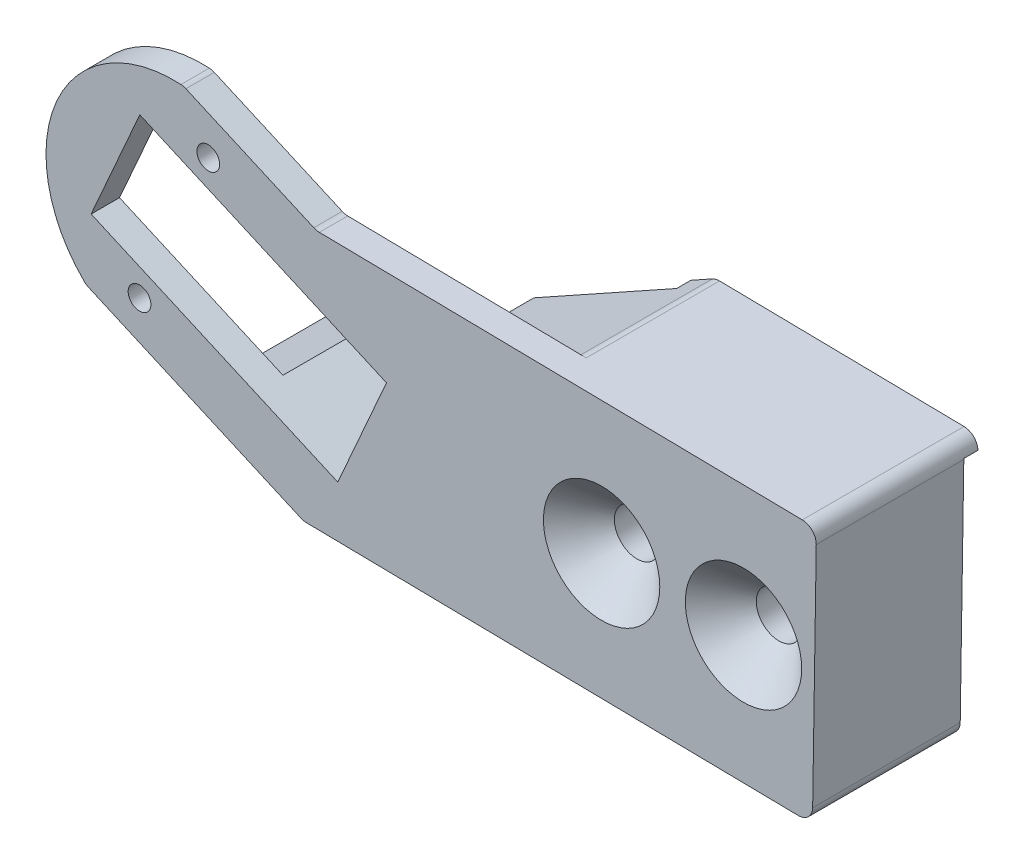
SolidWorks part; units mm, degrees
ref_plane "Front Plane" through (0, 0, 0) normal (0, 0, 1) x (1, 0, 0)
ref_plane "Top Plane" through (0, 0, 0) normal (0, 1, 0) x (1, 0, 0)
ref_plane "Right Plane" through (0, 0, 0) normal (1, 0, 0) x (0, 0, -1)
sketch "Sketch2" plane through (0, 0, 0) normal (0, 0, 1) x (1, 0, 0)
  line L0 (110.8747, 169.3007) -> (232.868, 168.0195) construction
  line L1 (231.4782, 167.9235) -> (111.8685, 169.7952)
  line L2 (109.9284, 170.22) -> (90.3522, 178.8568)
  line L3 (88.0797, 180.8644) -> (81.6243, 191.6546)
  line L4 (91.1154, 198.8867) -> (104.3747, 187.2622)
  line L5 (107.6071, 186.0223) -> (189.9391, 184.9726)
  line L6 (192.2834, 185.5226) -> (216.6587, 198.016)
  line L7 (218.9657, 198.5663) -> (266.2136, 198.3172)
  line L8 (233.9522, 168.5343) -> (269.7006, 188.0491)
  arc A0 (266.2136, 198.3172) -> (269.7006, 188.0491) centre (266.1834, 192.5808) cw
  arc A1 (81.6243, 191.6546) -> (91.1154, 198.8867) centre (86.7764, 194.737) cw
  circle A2 centre (91.5684, 182.2893) radius 1.1478 construction
  circle A3 centre (86.7764, 194.737) radius 1.0668 construction
  circle A4 centre (232.1221, 192.0862) radius 0.8742 construction
  circle A5 centre (266.1834, 192.5808) radius 1.1755 construction
  arc A6 (189.9391, 184.9726) -> (192.2834, 185.5226) centre (190.0028, 189.9722) ccw
  arc A7 (216.6587, 198.016) -> (218.9657, 198.5663) centre (218.9393, 193.5664) cw
  arc A8 (233.9522, 168.5343) -> (231.4782, 167.9235) centre (231.5564, 172.9229) cw
  arc A9 (109.9284, 170.22) -> (111.8685, 169.7952) centre (111.9467, 174.7946) ccw
  arc A10 (107.6071, 186.0223) -> (104.3747, 187.2622) centre (107.6709, 191.0219) cw
  arc A11 (90.3522, 178.8568) -> (88.0797, 180.8644) centre (92.3704, 183.4313) cw
  circle A12 centre (245.4018, 191.4665) radius 0.7725 construction
  circle A13 centre (245.2646, 181.5408) radius 0.6658 construction
  circle A14 centre (208.1864, 183.5188) radius 1.0221 construction
  circle A15 centre (86.7764, 194.737) radius 1.5
  circle A16 centre (91.5684, 182.2893) radius 2
  circle A17 centre (208.1864, 183.5188) radius 1.5
  circle A18 centre (232.1221, 192.0862) radius 1.5
  circle A20 centre (266.1834, 192.5808) radius 2
  dimension "D2" = 4
  dimension "D3" = 3
  dimension "D4" = 3
  dimension "D5" = 4
  dimension "D6" = 3
  dimension "D1" = 122
sketch "Sketch7" plane through (0, 0, 0) normal (0, 0, 1) x (1, 0, 0)
  line L0 (95.6805, 174.2681) -> (100.2651, 184.6595) construction
  line L1 (93.1156, 173.4092) -> (99.1703, 187.1329) construction
  line L2 (93.1156, 173.4092) -> (83.9665, 177.4457)
  line L3 (83.9665, 177.4457) -> (90.0212, 191.1694) construction
  line L4 (99.1703, 187.1329) -> (90.0212, 191.1694)
  line L5 (93.1156, 173.4092) -> (90.0212, 191.1694) construction
  line L6 (83.9665, 177.4457) -> (99.1703, 187.1329) construction
  line L7 (88.541, 175.4274) -> (94.5957, 189.1512) construction
  line L8 (111.8685, 169.7952) -> (231.4782, 167.9235)
  line L9 (233.9522, 168.5343) -> (269.7006, 188.0491)
  line L10 (266.2136, 198.3172) -> (218.9657, 198.5663)
  line L11 (216.6587, 198.016) -> (192.2834, 185.5226)
  line L12 (189.9391, 184.9726) -> (107.6071, 186.0223)
  line L13 (104.3747, 187.2622) -> (91.1154, 198.8867)
  line L14 (81.6243, 191.6546) -> (88.0797, 180.8644)
  line L15 (90.3522, 178.8568) -> (109.9284, 170.22)
  line L16 (111.8685, 169.7952) -> (231.4782, 167.9235) construction
  line L17 (233.9522, 168.5343) -> (269.7006, 188.0491) construction
  line L18 (266.2136, 198.3172) -> (218.9657, 198.5663) construction
  line L19 (216.6587, 198.016) -> (192.2834, 185.5226) construction
  line L20 (189.9391, 184.9726) -> (107.6071, 186.0223) construction
  line L21 (104.3747, 187.2622) -> (91.1154, 198.8867) construction
  line L22 (81.6243, 191.6546) -> (88.0797, 180.8644) construction
  line L23 (90.3522, 178.8568) -> (109.9284, 170.22) construction
  line L24 (86.9938, 184.3075) -> (96.143, 180.2711) construction
  line L25 (100.7006, 168.9698) -> (92.5965, 172.5452)
  line L26 (136.8555, 186.5959) -> (86.8555, 187.3783) construction
  line L27 (136.8555, 186.5959) -> (136.5709, 168.4085)
  line L28 (136.5709, 168.4085) -> (86.5709, 169.1909) construction
  line L29 (86.8555, 187.3783) -> (86.5709, 169.1909) construction
  line L30 (118.3569, 186.8853) -> (92.5965, 172.5452)
  line L31 (86.5709, 169.1909) -> (118.3569, 186.8853) construction
  line L32 (136.8555, 186.5959) -> (118.3569, 186.8853)
  line L33 (136.7132, 177.5022) -> (101.5011, 177.5022) construction
  line L34 (100.7006, 168.9698) -> (136.5709, 168.4085)
  circle A0 centre (91.5684, 182.2893) radius 9.0139
  circle A1 centre (91.5684, 182.2893) radius 2
  circle A2 centre (91.5684, 182.2893) radius 2 construction
  circle A3 centre (266.1834, 192.5808) radius 2
  circle A4 centre (266.1834, 192.5808) radius 2 construction
  circle A5 centre (232.1221, 192.0862) radius 1.5
  circle A6 centre (232.1221, 192.0862) radius 1.5 construction
  circle A7 centre (208.1864, 183.5188) radius 1.5
  circle A8 centre (208.1864, 183.5188) radius 1.5 construction
  circle A9 centre (86.7764, 194.737) radius 1.5
  circle A10 centre (86.7764, 194.737) radius 1.5 construction
  circle A11 centre (91.5684, 182.2893) radius 9.0139 construction
  arc A12 (83.9665, 177.4457) -> (90.0212, 191.1694) centre (91.5684, 182.2893) cw construction
  arc A13 (93.1156, 173.4092) -> (95.6805, 174.2681) centre (91.5684, 182.2893) ccw construction
  arc A14 (100.2651, 184.6595) -> (99.1703, 187.1329) centre (91.5684, 182.2893) ccw construction
  circle A15 centre (89.1465, 176.7998) radius 1
  circle A16 centre (93.9903, 187.7788) radius 1
  circle A17 centre (121.7126, 177.5022) radius 1.6
  arc A18 (231.4782, 167.9235) -> (233.9522, 168.5343) centre (231.5564, 172.9229) ccw
  arc A19 (269.7006, 188.0491) -> (266.2136, 198.3172) centre (266.1834, 192.5808) ccw
  arc A20 (218.9657, 198.5663) -> (216.6587, 198.016) centre (218.9393, 193.5664) ccw
  arc A21 (189.9391, 184.9726) -> (192.2834, 185.5226) centre (190.0028, 189.9722) ccw
  arc A22 (104.3747, 187.2622) -> (107.6071, 186.0223) centre (107.6709, 191.0219) ccw
  arc A23 (91.1154, 198.8867) -> (81.6243, 191.6546) centre (86.7764, 194.737) ccw
  arc A24 (88.0797, 180.8644) -> (90.3522, 178.8568) centre (92.3704, 183.4313) ccw
  arc A25 (109.9284, 170.22) -> (111.8685, 169.7952) centre (111.9467, 174.7946) ccw
  arc A26 (231.4782, 167.9235) -> (233.9522, 168.5343) centre (231.5564, 172.9229) ccw construction
  arc A27 (269.7006, 188.0491) -> (266.2136, 198.3172) centre (266.1834, 192.5808) ccw construction
  arc A28 (218.9657, 198.5663) -> (216.6587, 198.016) centre (218.9393, 193.5664) ccw construction
  arc A29 (189.9391, 184.9726) -> (192.2834, 185.5226) centre (190.0028, 189.9722) ccw construction
  arc A30 (104.3747, 187.2622) -> (107.6071, 186.0223) centre (107.6709, 191.0219) ccw construction
  arc A31 (91.1154, 198.8867) -> (81.6243, 191.6546) centre (86.7764, 194.737) ccw construction
  arc A32 (88.0797, 180.8644) -> (90.3522, 178.8568) centre (92.3704, 183.4313) ccw construction
  arc A33 (109.9284, 170.22) -> (111.8685, 169.7952) centre (111.9467, 174.7946) ccw construction
  circle A34 centre (131.7126, 177.5022) radius 1.6
  dimension "D10" = 2
  dimension "D13" = 3.2
  dimension "D14" = 3.2
  dimension "D7" = 15
  dimension "D8" = 10
  dimension "D9" = 2
  dimension "D11" = 1.5
  dimension "D12" = 1
  dimension "D15" = 10
  dimension "D16" = 5
  dimension "D17" = 1
  dimension "D18" = 2
  dimension "D19" = 50
  dimension "D20" = 150
  dimension "D1" = 0
  dimension "D2" = 0
  dimension "D3" = 0
  dimension "D4" = 0
  dimension "D5" = 0
  dimension "D6" = 0
extrude "Boss-Extrude4" add sketch "Sketch7" along normal blind 8.4 contours L25 L34 L27 L32 L30 A34 A17
sketch "Sketch8" plane through (0, 0, 8.4) normal (0, 0, 1) x (1, 0, 0)
  line L10 (99.1703, 187.1329) -> (90.0212, 191.1694) construction
  line L11 (93.1156, 173.4092) -> (83.9665, 177.4457) construction
  line L12 (99.1703, 187.1329) -> (90.0212, 191.1694) construction
  line L13 (93.1156, 173.4092) -> (83.9665, 177.4457) construction
  line L14 (99.1703, 187.1329) -> (90.0212, 191.1694) construction
  line L15 (101.6151, 187.1473) -> (136.8555, 186.5959)
  line L16 (136.8555, 186.5959) -> (136.5709, 168.4085)
  line L25 (93.1156, 173.4092) -> (83.9665, 177.4457) construction
  line L27 (101.6151, 187.1473) -> (92.2546, 191.277)
  line L32 (136.5709, 168.4085) -> (100.7006, 168.9698)
  line L33 (85.3926, 175.7235) -> (100.7006, 168.9698)
  arc A0 (92.2546, 191.277) -> (85.3926, 175.7235) centre (91.5684, 182.2893) ccw
  circle A1 centre (121.7126, 177.5022) radius 1.6
  circle A2 centre (121.7126, 177.5022) radius 1.6
  circle A3 centre (131.7126, 177.5022) radius 1.6
  circle A4 centre (131.7126, 177.5022) radius 1.6
  circle A5 centre (91.5684, 182.2893) radius 9.0139
  circle A6 centre (91.5684, 182.2893) radius 9.0139 construction
  circle A7 centre (93.9903, 187.7788) radius 0.8
  circle A8 centre (89.1465, 176.7998) radius 0.8
  circle A11 centre (93.9903, 187.7788) radius 1
  circle A12 centre (93.9903, 187.7788) radius 1 construction
  circle A13 centre (89.1465, 176.7998) radius 1
  circle A14 centre (89.1465, 176.7998) radius 1 construction
  dimension "D5" = 1.6
  dimension "D6" = 1.6
  dimension "D4" = 1
  dimension "D1" = 0
  dimension "D2" = 0
  dimension "D3" = 0
  dimension "D7" = 0
  dimension "D8" = 0
extrude "Boss-Extrude5" add sketch "Sketch8" along normal blind 2
sketch "Sketch9" plane through (0, 0, 0) normal (0, 0, -1) x (-1, 0, 0)
  line L0 (-136.8555, 186.5959) -> (-136.5709, 168.4085) construction
  line L1 (-118.3569, 186.8853) -> (-92.5965, 172.5452) construction
  line L2 (-136.8407, 185.6496) -> (-136.8555, 186.5959)
  line L3 (-136.8555, 186.5959) -> (-118.3569, 186.8853)
  line L4 (-118.3569, 186.8853) -> (-116.6006, 185.9076)
  line L8 (-231.4782, 167.9235) -> (-111.8685, 169.7952)
  line L9 (-269.7006, 188.0491) -> (-233.9522, 168.5343)
  line L10 (-218.9657, 198.5663) -> (-266.2136, 198.3172)
  line L11 (-192.2834, 185.5226) -> (-216.6587, 198.016)
  line L12 (-107.6071, 186.0223) -> (-189.9391, 184.9726)
  line L13 (-91.1154, 198.8867) -> (-104.3747, 187.2622)
  line L14 (-88.0797, 180.8644) -> (-81.6243, 191.6546)
  line L15 (-109.9284, 170.22) -> (-90.3522, 178.8568)
  line L20 (-116.6006, 185.9076) -> (-136.8407, 185.6496)
  arc A18 (-233.9522, 168.5343) -> (-231.4782, 167.9235) centre (-231.5564, 172.9229) ccw
  arc A19 (-266.2136, 198.3172) -> (-269.7006, 188.0491) centre (-266.1834, 192.5808) ccw
  arc A20 (-216.6587, 198.016) -> (-218.9657, 198.5663) centre (-218.9393, 193.5664) ccw
  arc A21 (-192.2834, 185.5226) -> (-189.9391, 184.9726) centre (-190.0028, 189.9722) ccw
  arc A22 (-107.6071, 186.0223) -> (-104.3747, 187.2622) centre (-107.6709, 191.0219) ccw
  arc A23 (-81.6243, 191.6546) -> (-91.1154, 198.8867) centre (-86.7764, 194.737) ccw
  arc A24 (-90.3522, 178.8568) -> (-88.0797, 180.8644) centre (-92.3704, 183.4313) ccw
  arc A25 (-111.8685, 169.7952) -> (-109.9284, 170.22) centre (-111.9467, 174.7946) ccw
  dimension "D6" = 0
extrude "Boss-Extrude6" add sketch "Sketch9" along normal blind 1
chamfer "Chamfer1" distance 2.5 angle 45 2 edges at (133.3126, 177.5022, 10.4) (123.3126, 177.5022, 10.4)
fillet "Fillet1" radius 1 7 edges at (92.2546, 191.277, 9.4) (85.3926, 175.7235, 9.4) (136.8555, 186.5959, 4.7) (136.5709, 168.4085, 5.2) (100.7006, 168.9698, 5.2) (101.6151, 187.1473, 9.4) (118.3569, 186.8853, 3.7)
sketch "Sketch10" plane through (0, 0, 10.4) normal (0, 0, 1) x (1, 0, 0)
  line L0 (93.9903, 187.7788) -> (89.1465, 176.7998) construction
  line L2 (93.97, 176.5845) -> (97.401, 184.3613) construction
  line L3 (93.97, 176.5845) -> (85.7358, 180.2173)
  line L4 (85.7358, 180.2173) -> (89.1668, 187.9941)
  line L5 (97.401, 184.3613) -> (89.1668, 187.9941)
  line L6 (93.97, 176.5845) -> (89.1668, 187.9941) construction
  line L7 (85.7358, 180.2173) -> (97.401, 184.3613) construction
  line L8 (101.4297, 187.2291) -> (92.4161, 191.2058) construction
  line L9 (97.401, 184.3613) -> (106.5501, 180.3248)
  line L10 (106.5501, 180.3248) -> (103.1191, 172.548)
  line L11 (103.1191, 172.548) -> (93.97, 176.5845)
  point P4 (91.5684, 182.2893)
  dimension "D1" = 8.5
  dimension "D2" = 9
  dimension "D3" = 10
extrude "Cut-Extrude1" cut sketch "Sketch10" against normal blind 20
